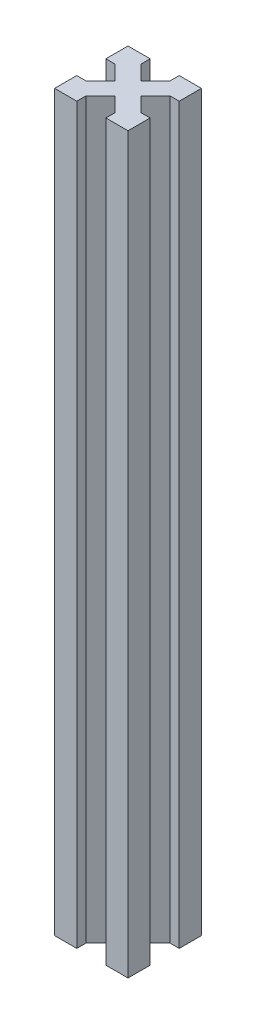
SolidWorks part; units mm, degrees
ref_plane "Plan de face" through (0, 0, 0) normal (0, 0, 1) x (1, 0, 0)
ref_plane "Plan de dessus" through (0, 0, 0) normal (0, 1, 0) x (1, 0, 0)
ref_plane "Plan de droite" through (0, 0, 0) normal (1, 0, 0) x (0, 0, -1)
sketch "Esquisse1" plane through (0, 0, 0) normal (0, 1, 0) x (1, 0, 0)
  line L0 (-2.5, 17.5) -> (-17.5, 17.5)
  line L1 (0, 0) -> (-20, 0)
  line L2 (0, 0) -> (0, 20)
  line L3 (0, 20) -> (-20, 20)
  line L4 (-20, 0) -> (-20, 20)
  line L5 (0, 20) -> (-20, 0) construction
  line L6 (-17.5, 2.5) -> (-17.5, 17.5)
  line L11 (-2.5, 2.5) -> (-17.5, 2.5)
  line L12 (-2.5, 2.5) -> (-2.5, 17.5)
  line L13 (-20, 20) -> (0, 0) construction
  line L14 (-26.9957, 23.4601) -> (-23.4601, 26.9957)
  line L15 (-26.9957, 23.4601) -> (3.4601, -6.9957)
  line L16 (-23.4601, 26.9957) -> (6.9957, -3.4601)
  line L17 (3.4601, -6.9957) -> (6.9957, -3.4601)
  line L18 (-26.9957, 23.4601) -> (6.9957, -3.4601) construction
  line L19 (-23.4601, 26.9957) -> (3.4601, -6.9957) construction
  line L20 (-10, 20) -> (-10, 0) construction
  line L21 (-23.4601, -6.9957) -> (-26.9957, -3.4601)
  line L22 (3.4601, 26.9957) -> (-26.9957, -3.4601)
  line L23 (6.9957, 23.4601) -> (-23.4601, -6.9957)
  line L24 (6.9957, 23.4601) -> (3.4601, 26.9957)
  line L25 (-17.5, 13.9645) -> (-20, 13.9645)
  line L26 (-20, 10) -> (0, 10) construction
  line L27 (-17.5, 6.0355) -> (-20, 6.0355)
  line L28 (-2.5, 6.0355) -> (0, 6.0355)
  line L29 (-2.5, 13.9645) -> (0, 13.9645)
  line L30 (-2.5, 6.0355) -> (0, 6.0355)
  line L31 (-2.5, 13.9645) -> (0, 13.9645)
  line L32 (-13.9645, 2.5) -> (-13.9645, 0)
  line L33 (-6.0355, 17.5) -> (-6.0355, 20)
  line L34 (-13.9645, 17.5) -> (-13.9645, 20)
  line L35 (-6.0355, 2.5) -> (-6.0355, 0)
  point P11 (-10, 10)
  dimension "D1" = 20
  dimension "D2" = 20
  dimension "D3" = 7.3934
  dimension "D4" = 2.5
  dimension "D5" = 43.071
  dimension "D6" = 2.5
extrude "Boss.-Extru.1" add sketch "Esquisse1" along normal blind 200 contours L15 L35 L1 | L16 L12 L11 L15 L1 L2 | L28 L16 L2 | L16 L23 L15 L11 L12 | L32 L23 L1 | L23 L11 L6 L22 L4 L1 | L22 L27 L4 | L23 L15 L22 L6 L11 | L23 L16 L22 L15 | L23 L12 L0 L22 L16 | L23 L2 L3 L22 L0 L12 | L23 L29 L2 | L33 L22 L3 | L16 L34 L3 | L16 L3 L4 L15 L6 L0 | L25 L15 L4 | L22 L16 L0 L6 L15
